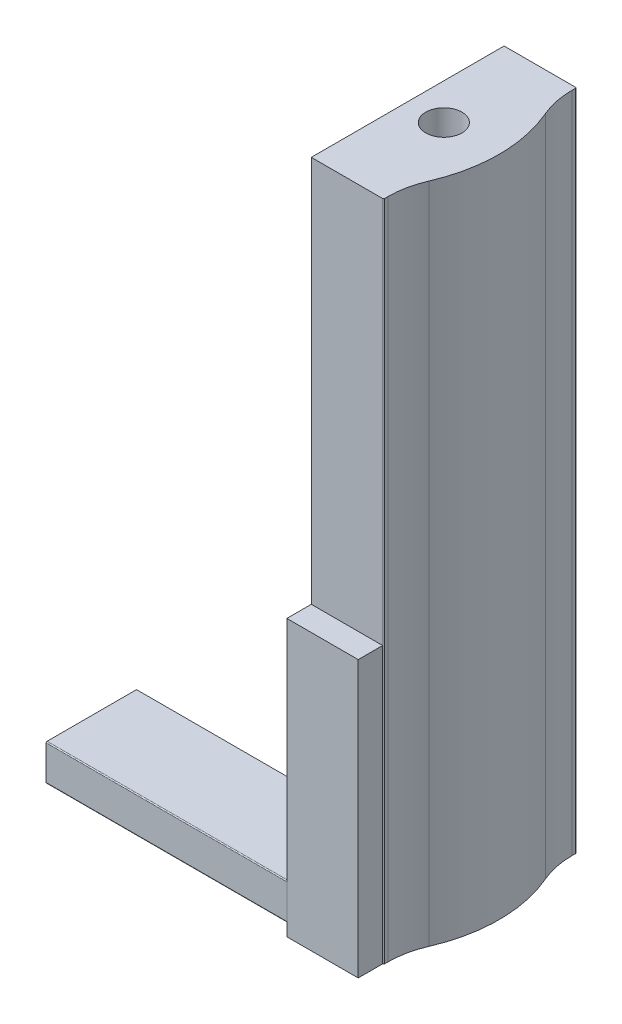
SolidWorks part; units mm, degrees
ref_plane "Front Plane" through (0, 0, 0) normal (0, 0, 1) x (1, 0, 0)
ref_plane "Top Plane" through (0, 0, 0) normal (0, 1, 0) x (1, 0, 0)
ref_plane "Right Plane" through (0, 0, 0) normal (1, 0, 0) x (0, 0, -1)
sketch "Sketch1" plane through (0, 0, 0) normal (0, 1, 0) x (1, 0, 0)
  line L15 (1.5001, 8.0105) -> (1.5001, 8.234)
  line L16 (-3.2624, -4.0056) -> (-3.2624, 7.9006)
  line L17 (-2.8655, -4.4025) -> (1.4366, -4.4025)
  line L18 (-2.8655, 8.2975) -> (1.4366, 8.2975)
  line L19 (1.5001, -4.339) -> (1.5001, -4.1155)
  line L20 (1.5001, 8.0105) -> (1.5001, 8.2975)
  line L21 (1.5001, -4.4025) -> (-3.2624, -4.4025)
  line L22 (1.5001, -4.4025) -> (1.5001, -4.1155)
  line L23 (1.5001, 8.2975) -> (-3.2624, 8.2975)
  line L24 (-3.2624, -4.4025) -> (-3.2624, 8.2975)
  arc A6 (1.9611, 5.7839) -> (1.9611, -1.8889) centre (-6.9066, 1.9475) cw
  circle A7 centre (-0.8811, 1.9475) radius 1.1906
  arc A8 (1.9611, -1.8889) -> (1.5001, -4.1155) centre (7.1078, -4.1155) ccw
  arc A9 (1.5001, 8.0105) -> (1.9611, 5.7839) centre (7.1078, 8.0105) ccw
  arc A12 (1.5001, -4.339) -> (1.4366, -4.4025) centre (1.4366, -4.339) cw
  arc A13 (1.4366, 8.2975) -> (1.5001, 8.234) centre (1.4366, 8.234) cw
  dimension "D1" = 5.6077
  dimension "D2" = 0.0635
extrude "Boss-Extrude4" add sketch "Sketch1" along normal blind 43.6562 contours A13 L18 L23 L24 L16 L21 L17 A12 L19 A8 A6 A9 L15 A7
sketch "Sketch6" plane through (-3.2624, 0, 0) normal (-1, 0, 0) x (0, 0, 1)
  line L1 (0.0369, 3.175) -> (5.9265, 3.175)
  line L2 (5.99, 3.1115) -> (5.99, 0.8573)
  line L3 (5.9265, 0.7937) -> (0.1004, 0.7937)
  line L4 (0.0369, 0.8572) -> (0.0369, 3.175)
  arc A0 (0.1004, 0.7937) -> (0.0369, 0.8572) centre (0.1004, 0.8572) cw
  arc A1 (5.99, 0.8573) -> (5.9265, 0.7937) centre (5.9265, 0.8572) cw
  arc A2 (5.99, 3.1115) -> (5.9265, 3.175) centre (5.9265, 3.1115) ccw
  dimension "D1" = 0.0635
  dimension "D2" = 0.0635
extrude "Boss-Extrude5" add sketch "Sketch6" along normal blind 15.875
sketch "Sketch7" plane through (0, 0, 0) normal (0, -1, 0) x (1, 0, 0)
  line L1 (-3.2624, 4.4025) -> (1.4369, 4.4025)
  line L2 (-3.2624, 4.4025) -> (-3.2624, 6.0118)
  line L3 (-3.2624, 6.0118) -> (1.4369, 6.0118)
  line L4 (1.4369, 4.4025) -> (1.4369, 6.0118)
extrude "Boss-Extrude6" add sketch "Sketch7" against normal blind 18.161
